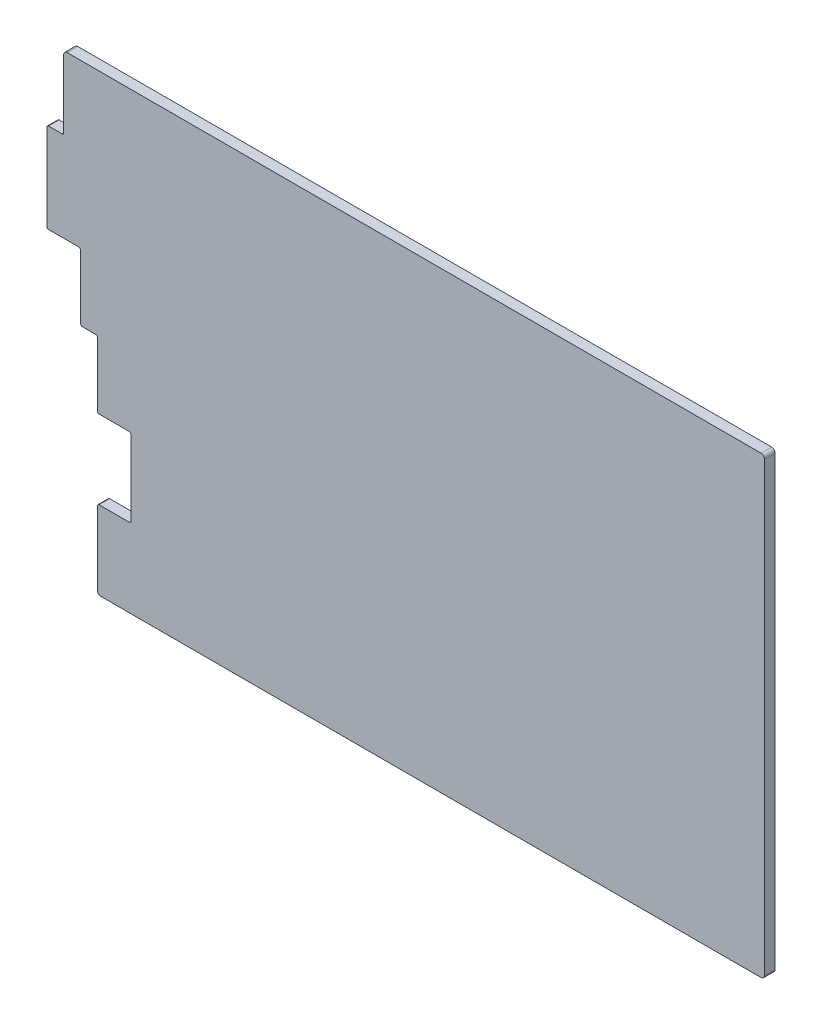
SolidWorks part; units mm, degrees
ref_plane "前视基准面" through (0, 0, 0) normal (0, 0, 1) x (1, 0, 0)
ref_plane "上视基准面" through (0, 0, 0) normal (0, 1, 0) x (1, 0, 0)
ref_plane "右视基准面" through (0, 0, 0) normal (1, 0, 0) x (0, 0, -1)
other "Configuration Table"
sketch "Model" plane through (0, 0, 0) normal (0, 0, 1) x (1, 0, 0)
  line L0 (4.8569, 129.021) -> (204.883, 129.021)
  line L1 (204.883, 129.021) -> (204.883, 0.4341)
  line L2 (204.883, 0.4341) -> (14.3819, 0.4341)
  line L3 (15.9819, 22.641) -> (15.9819, 0.4341)
  line L4 (25.5069, 22.641) -> (15.9819, 22.641)
  line L5 (25.5069, 44.891) -> (25.5069, 22.641)
  line L6 (15.9819, 44.891) -> (25.5069, 44.891)
  line L7 (15.9819, 63.941) -> (15.9819, 44.891)
  line L8 (11.2189, 63.941) -> (15.9819, 63.941)
  line L9 (11.2189, 82.991) -> (11.2189, 63.941)
  line L10 (1.6939, 82.991) -> (11.2189, 82.991)
  line L11 (1.6939, 82.991) -> (1.6939, 108.371)
  line L12 (1.6939, 108.371) -> (6.4569, 108.371)
  line L13 (6.4569, 108.371) -> (6.4569, 129.021)
  line L328 (0.0939, 81.391) -> (0.0939, 109.971)
  line L329 (14.3819, 24.241) -> (14.3819, 0.4341)
  line L435 (0.0939, 109.971) -> (4.8569, 109.971)
  line L436 (4.8569, 109.971) -> (4.8569, 129.021)
  line L437 (0.0939, 81.391) -> (9.6189, 81.391)
  line L438 (9.6189, 81.391) -> (9.6189, 62.341)
  line L439 (9.6189, 62.341) -> (14.3819, 62.341)
  line L440 (14.3819, 62.341) -> (14.3819, 43.291)
  line L441 (14.3819, 43.291) -> (23.9069, 43.291)
  line L442 (23.9069, 43.291) -> (23.9069, 24.241)
  line L443 (23.9069, 24.241) -> (14.3819, 24.241)
  dimension "D1" = 19.05
  dimension "D2" = 200.0261
  dimension "D3" = 28.58
  dimension "D4" = 9.525
  dimension "D5" = 4.763
  dimension "D6" = 1.6
extrude "凸台-拉伸1" add sketch "Model" along normal blind 3 contours L13 L12 L11 L10 L9 L8 L7 L6 L5 L4 L3 L2 L1 L0
fillet "圆角1" radius 0.5 10 edges at (15.9819, 22.641, 1.5) (25.5069, 22.641, 1.5) (15.9819, 44.891, 1.5) (25.5069, 44.891, 1.5) (15.9819, 63.941, 1.5) (11.2189, 63.941, 1.5) (1.6939, 82.991, 1.5) (11.2189, 82.991, 1.5) (1.6939, 108.371, 1.5) (6.4569, 108.371, 1.5)
fillet "圆角2" radius 1 4 edges at (204.883, 129.021, 1.5) (204.883, 0.4341, 1.5) (15.9819, 0.4341, 1.5) (6.4569, 129.021, 1.5)
